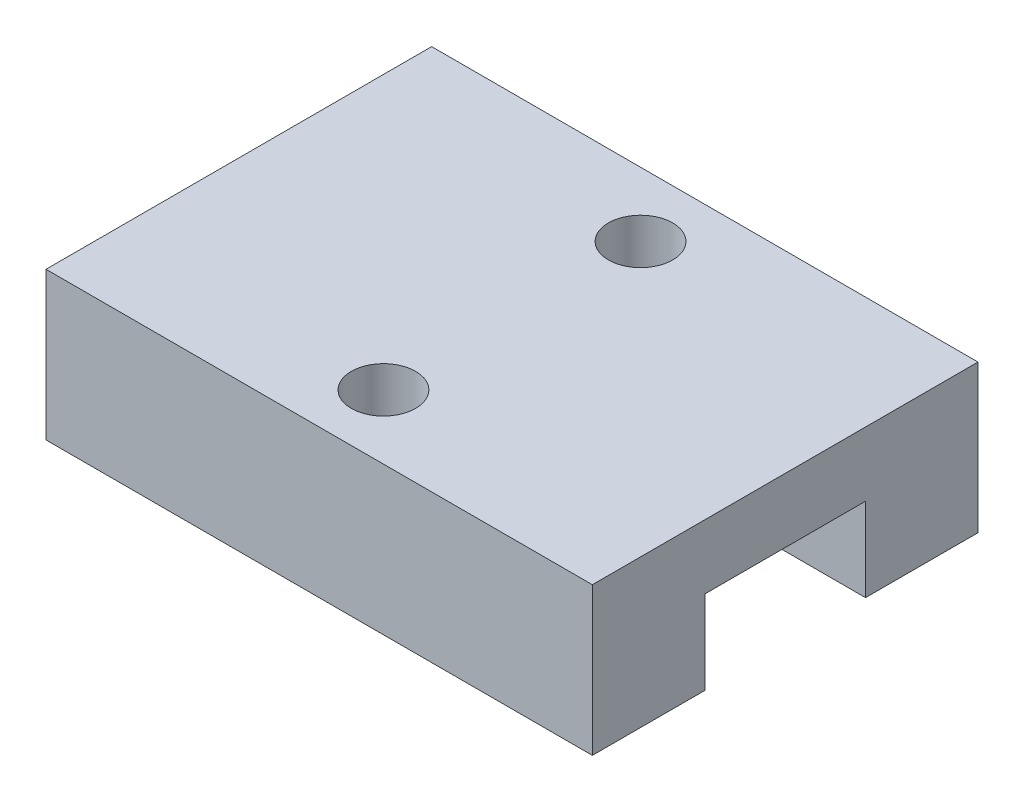
SolidWorks part; units mm, degrees
ref_plane "정면" through (0, 0, 0) normal (0, 0, 1) x (1, 0, 0)
ref_plane "윗면" through (0, 0, 0) normal (0, 1, 0) x (1, 0, 0)
ref_plane "우측면" through (0, 0, 0) normal (1, 0, 0) x (0, 0, -1)
sketch "스케치1" plane through (0, 0, 0) normal (0, 1, 0) x (1, 0, 0)
  line L1 (-8.5, 6) -> (8.5, 6)
  line L2 (-8.5, 6) -> (-8.5, -6)
  line L3 (-8.5, -6) -> (8.5, -6)
  line L4 (8.5, 6) -> (8.5, -6)
  point P4 (0, 6)
  point P6 (8.5, 0)
  dimension "D1" = 12
  dimension "D2" = 17
extrude "보스-돌출1" add sketch "스케치1" along normal blind 4.6
ref_plane "평면1" through (0, 2.6, 0) normal (0, 1, 0) x (1, 0, 0)
sketch "스케치3" plane through (0, 2.6, 0) normal (0, 1, 0) x (1, 0, 0)
  line L0 (8.5, -6) -> (8.5, 6) construction
  line L1 (8.5, 2.5) -> (-8.5, 2.5)
  line L2 (8.5, 2.5) -> (8.5, -2.5)
  line L3 (8.5, -2.5) -> (-8.5, -2.5)
  line L4 (-8.5, 2.5) -> (-8.5, -2.5)
  line L5 (-8.5, 6) -> (-8.5, -6) construction
  point P8 (8.5, 0)
  dimension "D1" = 5
extrude "컷-돌출1" cut sketch "스케치3" against normal up to surface (2.6 mm away) up to face at (0, 0, 0)
sketch "스케치4" plane through (0, 4.6, 0) normal (0, 1, 0) x (1, 0, 0)
  circle A0 centre (0, 4) radius 1
  circle A1 centre (0, -4) radius 1
  dimension "D1" = 2
  dimension "D2" = 2
  dimension "D3" = 8
  dimension "D4" = 4
extrude "컷-돌출2" cut sketch "스케치4" against normal blind 2
